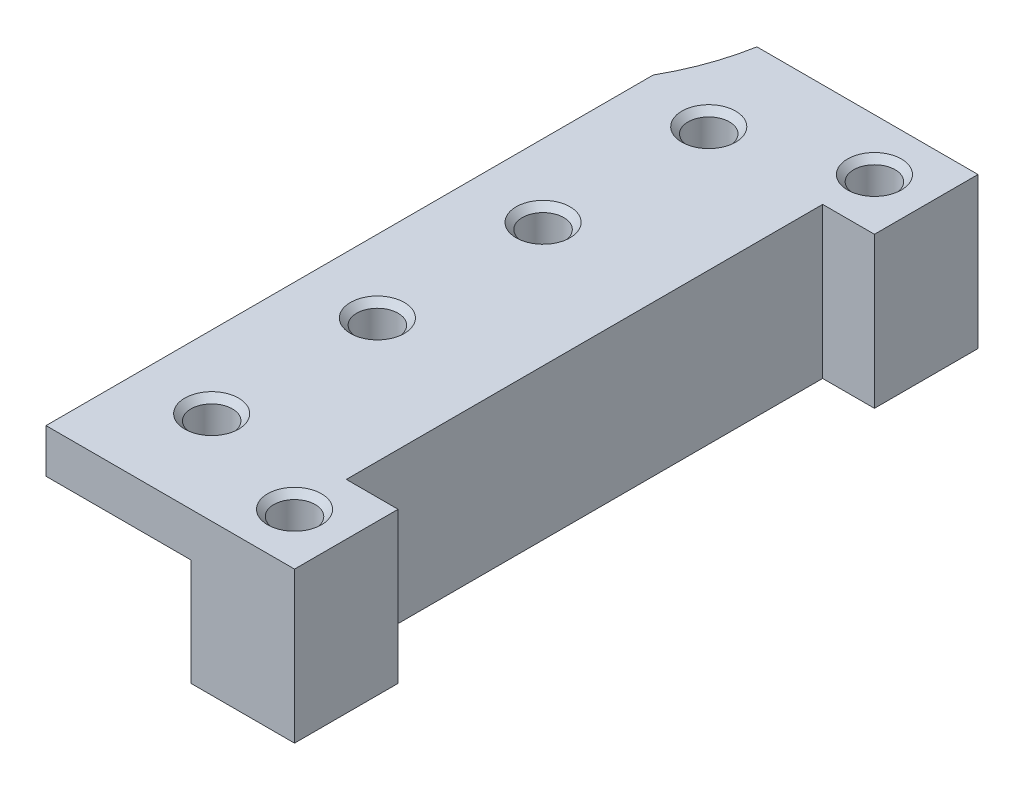
SolidWorks part; units mm, degrees
material "ABS"
ref_plane "Ön Düzlem" through (0, 0, 0) normal (0, 0, 1) x (1, 0, 0)
ref_plane "Üst Düzlem" through (0, 0, 0) normal (0, 1, 0) x (1, 0, 0)
ref_plane "Sağ Düzlem" through (0, 0, 0) normal (1, 0, 0) x (0, 0, -1)
sketch "Çizim3" plane through (0, 0, 0) normal (0, 1, 0) x (1, 0, 0)
  line L0 (16, 11.5) -> (19.5, 11.5)
  line L1 (-16, 25) -> (16, 25)
  line L2 (-16, 25) -> (-16, -25)
  line L3 (-16, -25) -> (16, -25)
  line L4 (16, 25) -> (16, -25)
  line L5 (-16, 25) -> (16, -25) construction
  line L6 (-16, -25) -> (16, 25) construction
  line L7 (16, -21.5) -> (10, -21.5)
  line L8 (16, -21.5) -> (16, 11.5)
  line L9 (16, 11.5) -> (10, 11.5)
  line L10 (10, -21.5) -> (10, 11.5)
  line L11 (19.5, 11.5) -> (19.5, -21.5)
  line L12 (19.5, -21.5) -> (16, -21.5)
  line L14 (16, 11.5) -> (22, 11.5)
  line L15 (16, 11.5) -> (16, 6.5)
  line L16 (16, 6.5) -> (22, 6.5)
  line L17 (22, 11.5) -> (22, 6.5)
  line L18 (16, -21.5) -> (22, -21.5)
  line L19 (16, -21.5) -> (16, -16.5)
  line L20 (16, -16.5) -> (22, -16.5)
  line L21 (22, -21.5) -> (22, -16.5)
  line L22 (16, 6.5) -> (19.5, 6.5)
  line L23 (16, 6.5) -> (16, -16.5)
  line L24 (16, -16.5) -> (19.5, -16.5)
  line L25 (19.5, 6.5) -> (19.5, -16.5)
  circle A0 centre (0, 13.5) radius 11
  circle A1 centre (0, 13.5) radius 11.5
  point P0 (0, 0)
  dimension "D3" = 22
  dimension "D8" = 23
  dimension "D1" = 32
  dimension "D2" = 50
  dimension "D4" = 11.5
  dimension "D5" = 6
  dimension "D6" = 13.5
  dimension "D7" = 33
  dimension "D9" = 3.5
  dimension "D10" = 6
  dimension "D11" = 5
  dimension "D12" = 5
  dimension "D13" = 6
  dimension "D14" = 3.5
extrude "Yükseklik-Ekstrüzyon3" add sketch "Çizim3" along normal blind 8.28 contours A1 L10 L7 L4 L8 L9 | L8 L20 L11 L16 | L4 L16 L11 L0 | L17 L14 L11 L16 | L20 L4 L12 L11 | L18 L21 L20 L11
sketch "Çizim4" plane through (0, 0, 21.5) normal (0, 0, 1) x (1, 0, 0)
  line L1 (10, 0) -> (17, 0)
  line L2 (10, 0) -> (10, 5.16)
  line L3 (10, 5.16) -> (17, 5.16)
  line L4 (17, 0) -> (17, 5.16)
  dimension "D1" = 5.16
  dimension "D2" = 7
extrude "Kes-Ekstrüzyon1" cut sketch "Çizim4" against normal through all
sketch "Vida Deliği Ref." plane through (0, 8.28, 0) normal (0, 1, 0) x (1, 0, 0)
  line L0 (19.5, 6.5) -> (19.5, -16.5) construction
  line L1 (22, 11.5) -> (11.3248, 11.5) construction
  line L2 (22, 11.5) -> (22, 6.5) construction
  line L3 (22, -21.5) -> (22, -16.5) construction
  line L4 (22, -21.5) -> (10, -21.5) construction
  point P0 (13.5, 7)
  point P1 (13.5, -1)
  point P2 (13.5, -9)
  point P3 (13.5, -17)
  point P8 (19.5, 9)
  point P9 (19.5, -19)
  dimension "D1" = 6
  dimension "D2" = 4.5
  dimension "D3" = 8
  dimension "D4" = 8
  dimension "D5" = 8
  dimension "D6" = 2.5
  dimension "D7" = 2.5
  dimension "D8" = 2.5
  dimension "D9" = 2.5
sketch "Çizim11" plane through (0, 8.28, 0) normal (0, 1, 0) x (1, 0, 0)
  line L0 (22, 11.5) -> (11.3248, 11.5) construction
  line L9 (22, -21.5) -> (10, -21.5)
  line L10 (22, -21.5) -> (22, 11.5)
  line L11 (22, 11.5) -> (10, 11.5)
  line L12 (10, -21.5) -> (10, 11.5)
  dimension "D1" = 12
extrude "Kes-Ekstrüzyon2" cut sketch "Çizim11" against normal blind 1
sketch "Vida Deliği Ref_2" plane through (0, 7.28, 0) normal (0, 1, 0) x (1, 0, 0)
  point P0 (13.5, 7)
  point P1 (19.5, -19)
  point P2 (19.5, 9)
  point P4 (13.5, -1)
  point P7 (13.5, -9)
  point P9 (13.5, -17)
hole_wizard "M2 Düz Başlı Makine Vidası İçin Havşa_ DEĞİŞTİREBİLİRİZ" positions "3B Çizim8" profile "Çizim15" countersink size "M2" standard "ANSI Metrik" end condition through all
sketch3d "3B Çizim8"
  point P0 (19.5, 7.28, 19)
  point P3 (19.5, 7.28, -9)
  point P6 (13.5, 7.28, 17)
  point P9 (13.5, 7.28, 9)
  point P12 (13.5, 7.28, 1)
  point P15 (13.5, 7.28, -7)
sketch "Çizim15" plane through (19.5, 7.28, 19) normal (1, 0, 0) x (0, 0, 1)
  line L0 (0, 0) -> (0, 7.28)
  line L1 (0, 7.28) -> (1, 7.28)
  line L2 (1, 7.28) -> (1, 0.3)
  line L3 (1, 0.3) -> (1.3, 0)
  line L5 (1.3, 0) -> (0, 0)
  line L6 (-1, 0.3) -> (-1.3, 0) construction
  line L11 (0, -6.35) -> (0, 107.95) construction
  dimension "Thru Hole Dia." = 2
  dimension "Thru Hole Depth" = 7.28
  dimension "Near C'Sink Dia." = 2.6
  dimension "Near C'Sink Angle" = 90
